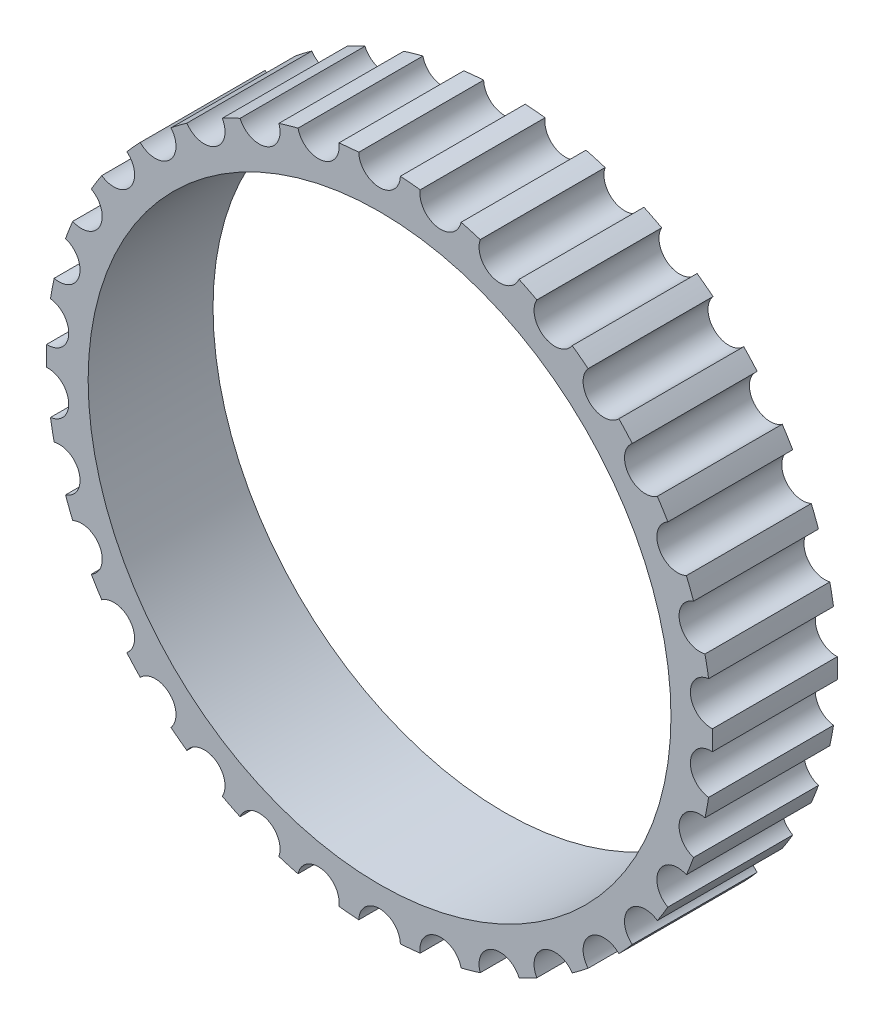
SolidWorks part; units mm, degrees
ref_plane "前视基准面" through (0, 0, 0) normal (0, 0, 1) x (1, 0, 0)
ref_plane "上视基准面" through (0, 0, 0) normal (0, 1, 0) x (1, 0, 0)
ref_plane "右视基准面" through (0, 0, 0) normal (1, 0, 0) x (0, 0, -1)
other "Configuration Table"
sketch "Sketch1" plane through (0, 0, 0) normal (0, 0, 1) x (1, 0, 0)
  circle A0 centre (0, 0) radius 7
  arc A1 (-0.4998, 7.9844) -> (-0.9759, 7.9403) centre (0, 0) ccw
  arc A2 (-0.4998, 7.9844) -> (0.4998, 7.9844) centre (0, 8) ccw
  arc A3 (0.9759, 7.9403) -> (1.9584, 7.7566) centre (1.47, 7.8638) ccw
  arc A4 (2.4183, 7.6257) -> (3.3503, 7.2647) centre (2.8899, 7.4598) ccw
  arc A5 (3.7783, 7.0515) -> (4.6281, 6.5254) centre (4.2115, 6.8017) ccw
  arc A6 (5.0097, 6.2372) -> (5.7484, 5.5638) centre (5.3896, 5.9121) ccw
  arc A7 (6.0705, 5.2105) -> (6.6728, 4.4128) centre (6.3841, 4.8211) ccw
  arc A8 (6.9246, 4.0063) -> (7.3701, 3.1116) centre (7.1613, 3.5659) ccw
  arc A9 (7.5428, 2.6657) -> (7.8163, 1.7043) centre (7.6946, 2.1893) ccw
  arc A10 (7.9042, 1.2343) -> (7.9964, 0.2391) centre (7.9659, 0.7381) ccw
  arc A11 (7.9964, -0.2391) -> (7.9042, -1.2343) centre (7.9659, -0.7381) ccw
  arc A12 (7.8163, -1.7043) -> (7.5428, -2.6657) centre (7.6946, -2.1893) ccw
  arc A13 (7.3701, -3.1116) -> (6.9246, -4.0063) centre (7.1613, -3.5659) ccw
  arc A14 (6.6728, -4.4128) -> (6.0705, -5.2105) centre (6.3841, -4.8211) ccw
  arc A15 (5.7484, -5.5638) -> (5.0097, -6.2372) centre (5.3896, -5.9121) ccw
  arc A16 (4.6281, -6.5254) -> (3.7783, -7.0515) centre (4.2115, -6.8017) ccw
  arc A17 (3.3503, -7.2647) -> (2.4183, -7.6257) centre (2.8899, -7.4598) ccw
  arc A18 (1.9584, -7.7566) -> (0.9759, -7.9403) centre (1.47, -7.8638) ccw
  arc A19 (0.4998, -7.9844) -> (-0.4998, -7.9844) centre (0, -8) ccw
  arc A20 (-0.9759, -7.9403) -> (-1.9584, -7.7566) centre (-1.47, -7.8638) ccw
  arc A21 (-2.4183, -7.6257) -> (-3.3503, -7.2647) centre (-2.8899, -7.4598) ccw
  arc A22 (-3.7783, -7.0515) -> (-4.6281, -6.5254) centre (-4.2115, -6.8017) ccw
  arc A23 (-5.0097, -6.2372) -> (-5.7484, -5.5638) centre (-5.3896, -5.9121) ccw
  arc A24 (-6.0705, -5.2105) -> (-6.6728, -4.4128) centre (-6.3841, -4.8211) ccw
  arc A25 (-6.9246, -4.0063) -> (-7.3701, -3.1116) centre (-7.1613, -3.5659) ccw
  arc A26 (-7.5428, -2.6657) -> (-7.8163, -1.7043) centre (-7.6946, -2.1893) ccw
  arc A27 (-7.9042, -1.2343) -> (-7.9964, -0.2391) centre (-7.9659, -0.7381) ccw
  arc A28 (-7.9964, 0.2391) -> (-7.9042, 1.2343) centre (-7.9659, 0.7381) ccw
  arc A29 (-7.8163, 1.7043) -> (-7.5428, 2.6657) centre (-7.6946, 2.1893) ccw
  arc A30 (-7.3701, 3.1116) -> (-6.9246, 4.0063) centre (-7.1613, 3.5659) ccw
  arc A31 (-6.6728, 4.4128) -> (-6.0705, 5.2105) centre (-6.3841, 4.8211) ccw
  arc A32 (-5.7484, 5.5638) -> (-5.0097, 6.2372) centre (-5.3896, 5.9121) ccw
  arc A33 (-4.6281, 6.5254) -> (-3.7783, 7.0515) centre (-4.2115, 6.8017) ccw
  arc A34 (-3.3503, 7.2647) -> (-2.4183, 7.6257) centre (-2.8899, 7.4598) ccw
  arc A35 (-1.9584, 7.7566) -> (-0.9759, 7.9403) centre (-1.47, 7.8638) ccw
  arc A36 (-4.6281, 6.5254) -> (-5.0097, 6.2372) centre (0, 0) ccw
  arc A37 (-5.7484, 5.5638) -> (-6.0705, 5.2105) centre (0, 0) ccw
  arc A38 (-6.6728, 4.4128) -> (-6.9246, 4.0063) centre (0, 0) ccw
  arc A39 (-7.3701, 3.1116) -> (-7.5428, 2.6657) centre (0, 0) ccw
  arc A40 (-7.8163, 1.7043) -> (-7.9042, 1.2343) centre (0, 0) ccw
  arc A41 (-7.9964, 0.2391) -> (-7.9964, -0.2391) centre (0, 0) ccw
  arc A42 (-7.9042, -1.2343) -> (-7.8163, -1.7043) centre (0, 0) ccw
  arc A43 (-7.5428, -2.6657) -> (-7.3701, -3.1116) centre (0, 0) ccw
  arc A44 (-6.9246, -4.0063) -> (-6.6728, -4.4128) centre (0, 0) ccw
  arc A45 (-6.0705, -5.2105) -> (-5.7484, -5.5638) centre (0, 0) ccw
  arc A46 (-5.0097, -6.2372) -> (-4.6281, -6.5254) centre (0, 0) ccw
  arc A47 (-3.7783, -7.0515) -> (-3.3503, -7.2647) centre (0, 0) ccw
  arc A48 (-0.9759, -7.9403) -> (-0.4998, -7.9844) centre (0, 0) ccw
  arc A49 (-2.4183, -7.6257) -> (-1.9584, -7.7566) centre (0, 0) ccw
  arc A50 (0.4998, -7.9844) -> (0.9759, -7.9403) centre (0, 0) ccw
  arc A51 (1.9584, -7.7566) -> (2.4183, -7.6257) centre (0, 0) ccw
  arc A52 (3.3503, -7.2647) -> (3.7783, -7.0515) centre (0, 0) ccw
  arc A53 (4.6281, -6.5254) -> (5.0097, -6.2372) centre (0, 0) ccw
  arc A54 (5.7484, -5.5638) -> (6.0705, -5.2105) centre (0, 0) ccw
  arc A55 (6.6728, -4.4128) -> (6.9246, -4.0063) centre (0, 0) ccw
  arc A56 (7.3701, -3.1116) -> (7.5428, -2.6657) centre (0, 0) ccw
  arc A57 (7.8163, -1.7043) -> (7.9042, -1.2343) centre (0, 0) ccw
  arc A58 (0.9759, 7.9403) -> (0.4998, 7.9844) centre (0, 0) ccw
  arc A59 (2.4183, 7.6257) -> (1.9584, 7.7566) centre (0, 0) ccw
  arc A60 (3.7783, 7.0515) -> (3.3503, 7.2647) centre (0, 0) ccw
  arc A61 (5.0097, 6.2372) -> (4.6281, 6.5254) centre (0, 0) ccw
  arc A62 (6.0705, 5.2105) -> (5.7484, 5.5638) centre (0, 0) ccw
  arc A63 (6.9246, 4.0063) -> (6.6728, 4.4128) centre (0, 0) ccw
  arc A64 (7.5428, 2.6657) -> (7.3701, 3.1116) centre (0, 0) ccw
  arc A65 (7.9042, 1.2343) -> (7.8163, 1.7043) centre (0, 0) ccw
  arc A66 (7.9964, -0.2391) -> (7.9964, 0.2391) centre (0, 0) ccw
  arc A67 (-1.9584, 7.7566) -> (-2.4183, 7.6257) centre (0, 0) ccw
  arc A68 (-3.3503, 7.2647) -> (-3.7783, 7.0515) centre (0, 0) ccw
  point P107 (0, 0)
  dimension "D1" = 14
  dimension "D2" = 16
  dimension "D3" = 1
  dimension "D4" = 34
extrude "Boss-Extrude1" add sketch "Sketch1" along normal blind 3
